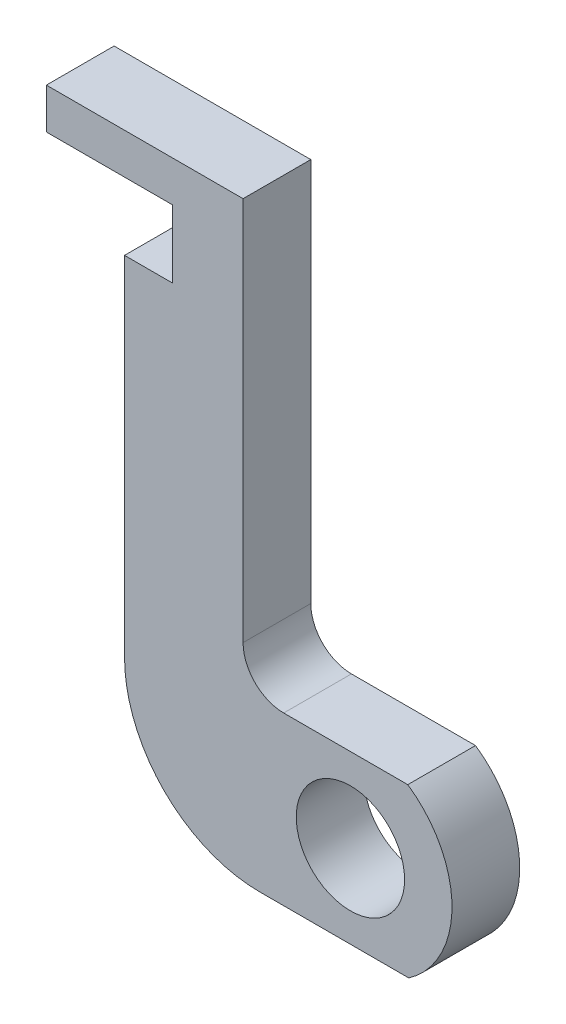
SolidWorks part; units mm, degrees
ref_plane "前视基准面" through (0, 0, 0) normal (0, 0, 1) x (1, 0, 0)
ref_plane "上视基准面" through (0, 0, 0) normal (0, 1, 0) x (1, 0, 0)
ref_plane "右视基准面" through (0, 0, 0) normal (1, 0, 0) x (0, 0, -1)
sketch "草图1" plane through (0, 0, 0) normal (0, 0, 1) x (1, 0, 0)
  line L0 (-7.9249, 37.5743) -> (-22.4465, 37.5743)
  line L1 (-22.4465, 37.5743) -> (-22.4465, 34.5743)
  line L2 (-22.4465, 34.5743) -> (-13.1445, 34.5743)
  line L3 (-13.1445, 34.5743) -> (-13.1445, 29.5743)
  line L4 (-13.1445, 29.5743) -> (-16.6759, 29.5743)
  line L5 (-16.6759, 29.5743) -> (-16.6759, 3.8647)
  line L6 (-6.6759, -6.1353) -> (4.3138, -6.1353)
  line L7 (-7.9249, 37.5743) -> (-7.9249, 9.1887)
  line L8 (-4.9249, 6.1887) -> (4.2368, 6.1887)
  circle A0 centre (0, 0) radius 4
  arc A1 (4.3138, -6.1353) -> (4.2368, 6.1887) centre (0, 0) ccw
  arc A2 (-16.6759, 3.8647) -> (-6.6759, -6.1353) centre (-6.6759, 3.8647) ccw
  arc A3 (-7.9249, 9.1887) -> (-4.9249, 6.1887) centre (-4.9249, 9.1887) ccw
  point P5 (-28.6882, 18.0065)
  point P14 (-30.808, -7.5)
  point P15 (-24.5663, 11.8826)
  point P16 (-35.5187, 16.5933)
  point P17 (-9.9632, 22.0106)
  point P18 (-20.0912, -7.5)
  point P19 (-14.3206, 13.7669)
  point P20 (-22.4465, 20.0086)
  point P21 (-9.9632, 7.5)
  point P22 (0, 0)
  point P23 (-5.8413, 22.4817)
  point P24 (-10.552, 14.238)
  point P25 (-16.6759, -7.5)
  point P30 (-4.9249, 4.8118)
  point P31 (-13.1445, 14.1555)
  point P32 (3.0058, 6.8713)
  point P33 (0, 0)
  point P34 (4.3138, -6.1353)
  point P35 (0, 0)
  point P36 (1.9509, 7.2418)
  point P37 (4.3138, 6.1887)
  dimension "D1" = 8
  dimension "D2" = 15
  dimension "D3" = 5
  dimension "D5" = 10
  dimension "D6" = 3
  dimension "D4" = 3
extrude "凸台-拉伸1" add sketch "草图1" along normal blind 5
